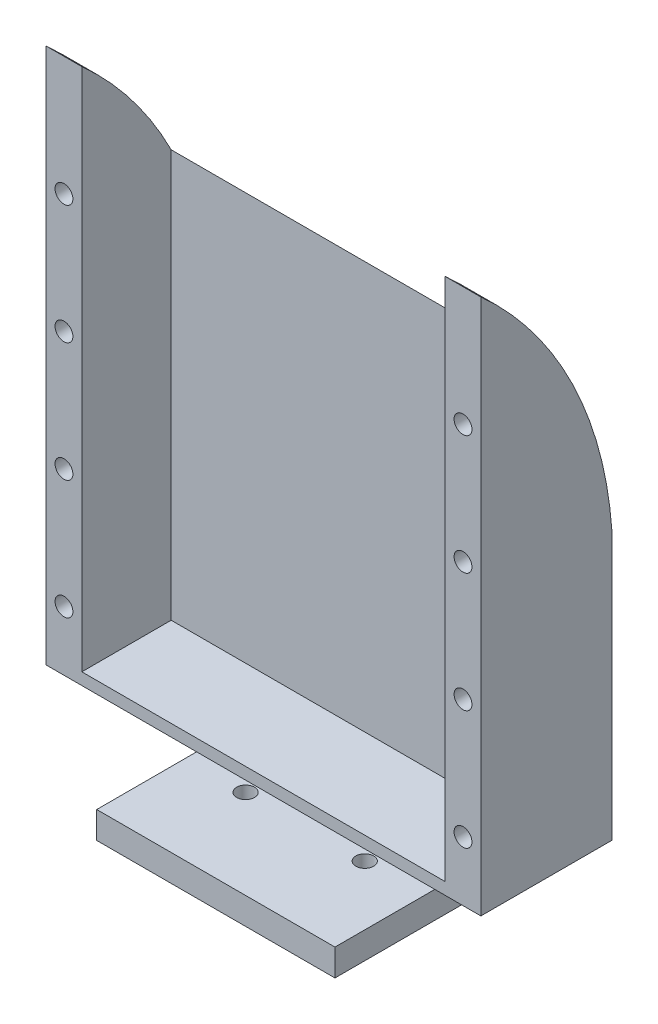
SolidWorks part; units mm, degrees
ref_plane "前视基准面" through (0, 0, 0) normal (0, 0, 1) x (1, 0, 0)
ref_plane "上视基准面" through (0, 0, 0) normal (0, 1, 0) x (1, 0, 0)
ref_plane "右视基准面" through (0, 0, 0) normal (1, 0, 0) x (0, 0, -1)
sketch "草图1" plane through (0, 0, 0) normal (0, 1, 0) x (1, 0, 0)
  line L0 (-10, 0) -> (10, 0) construction
  line L1 (-20, -15) -> (20, -15)
  line L2 (-20, -15) -> (-20, 15)
  line L3 (-20, 15) -> (20, 15)
  line L4 (20, -15) -> (20, 15)
  line L5 (-20, -15) -> (20, 15) construction
  line L6 (-20, 15) -> (20, -15) construction
  circle A2 centre (-10, 0) radius 1.5
  circle A3 centre (10, 0) radius 1.5
  point P0 (0, 0)
  point P9 (0, 0)
  dimension "D3" = 20
  dimension "D4" = 3
  dimension "D5" = 3
  dimension "D1" = 40
  dimension "D2" = 30
extrude "凸台-拉伸1" add sketch "草图1" along normal blind 4.5
sketch "草图2" plane through (0, 4.5, 0) normal (0, 1, 0) x (1, 0, 0)
  circle A0 centre (-10, 0) radius 3.5
  circle A1 centre (10, 0) radius 3.5
  dimension "D1" = 7
  dimension "D2" = 7
sketch "草图3" plane through (0, 0, -15) normal (0, 0, -1) x (-1, 0, 0)
  line L0 (0, 4.5) -> (0, 103.27) construction
  line L2 (-20, 4.5) -> (-20, 13.27)
  line L4 (20, 4.5) -> (20, 13.27)
  line L5 (0, 20.77) -> (0, 0) construction
  line L6 (-10, 8.27) -> (10, 8.27) construction
  line L7 (-20, 4.5) -> (20, 4.5) construction
  line L8 (-20, 4.5) -> (20, 4.5)
  line L9 (-36.5, 13.27) -> (-20, 13.27) construction
  line L10 (20, 13.27) -> (27.5, 13.27) construction
  line L11 (-36.5, 13.27) -> (-20, 13.27)
  line L12 (-36.5, 13.27) -> (-36.5, 103.27)
  line L13 (-36.5, 103.27) -> (36.5, 103.27)
  line L14 (36.5, 13.27) -> (36.5, 103.27)
  line L15 (20, 13.27) -> (36.5, 13.27)
  circle A0 centre (-10, 8.27) radius 1.5
  circle A1 centre (10, 8.27) radius 1.5
  point P11 (0, 8.27)
  point P20 (0, 20.77)
  dimension "D4" = 3
  dimension "D5" = 3
  dimension "D1" = 5
  dimension "D2" = 20
  dimension "D3" = 3.77
  dimension "D7" = 90
  dimension "D8" = 73
extrude "凸台-拉伸2" add sketch "草图3" against normal blind 7
sketch "草图4" plane through (0, 0, -8) normal (0, 0, 1) x (1, 0, 0)
  circle A0 centre (-10, 8.27) radius 3.5
  circle A1 centre (10, 8.27) radius 3.5
  dimension "D1" = 7
  dimension "D2" = 7
extrude "切除-拉伸2" cut sketch "草图4" against normal blind 3
sketch "草图6" plane through (0, 0, -8) normal (0, 0, 1) x (1, 0, 0)
  line L0 (-36.5, 103.27) -> (-36.5, 13.27)
  line L1 (-36.5, 13.27) -> (36.5, 13.27)
  line L2 (36.5, 13.27) -> (36.5, 103.27)
  line L3 (-30.5, 103.27) -> (-30.5, 15.27)
  line L4 (-36.5, 103.27) -> (36.5, 103.27) construction
  line L5 (30.5, 103.27) -> (30.5, 15.27)
  line L6 (-36.5, 103.27) -> (-30.5, 103.27)
  line L7 (30.5, 103.27) -> (36.5, 103.27)
  line L8 (-30.5, 15.27) -> (30.5, 15.27)
  dimension "D1" = 6
  dimension "D2" = 6
  dimension "D3" = 2
extrude "凸台-拉伸3" add sketch "草图6" along normal blind 15
sketch "草图7" plane through (0, 0, 7) normal (0, 0, 1) x (1, 0, 0)
  line L0 (-33.5, 103.27) -> (-33.5, 13.27) construction
  line L1 (-30.5, 103.27) -> (-36.5, 103.27) construction
  line L2 (-36.5, 13.27) -> (36.5, 13.27) construction
  line L3 (33.5, 103.27) -> (33.5, 13.27) construction
  line L4 (36.5, 103.27) -> (30.5, 103.27) construction
  line L5 (-36.5, 83.27) -> (36.5, 83.27) construction
  line L6 (-36.5, 103.27) -> (-36.5, 13.27) construction
  line L7 (36.5, 13.27) -> (36.5, 103.27) construction
  line L8 (-30.5, 103.27) -> (30.5, 103.27) construction
  line L9 (0, 103.27) -> (0, 25.387) construction
  line L10 (-36.5, 63.27) -> (36.5, 63.27) construction
  line L11 (-36.5, 43.27) -> (36.5, 43.27) construction
  line L12 (-36.5, 23.27) -> (36.5, 23.27) construction
  circle A0 centre (-33.5, 83.27) radius 1.5
  circle A1 centre (-33.5, 63.27) radius 1.5
  circle A2 centre (-33.5, 43.27) radius 1.5
  circle A5 centre (33.5, 43.27) radius 1.5
  circle A6 centre (33.5, 63.27) radius 1.5
  circle A7 centre (33.5, 83.27) radius 1.5
  circle A8 centre (-33.5, 23.27) radius 1.5
  circle A9 centre (33.5, 23.27) radius 1.5
  dimension "D5" = 3
  dimension "D1" = 20
  dimension "D2" = 20
  dimension "D3" = 40
  dimension "D4" = 60
extrude "切除-拉伸3" cut sketch "草图7" against normal blind 8
sketch "草图8" plane through (36.5, 0, 0) normal (1, 0, 0) x (0, 0, -1)
  line L0 (4, 103.27) -> (4, 13.27) construction
  line L1 (-7, 103.27) -> (15, 103.27) construction
  line L2 (-7, 13.27) -> (15, 13.27) construction
  circle A0 centre (4, 93.27) radius 1.5
  circle A1 centre (4, 83.27) radius 1.5
  circle A2 centre (4, 73.27) radius 1.5
  circle A3 centre (4, 63.27) radius 1.5
  circle A4 centre (4, 53.27) radius 1.5
  circle A5 centre (4, 43.27) radius 1.5
  circle A6 centre (4, 33.27) radius 1.5
  circle A7 centre (4, 23.27) radius 1.5
  dimension "D1" = 3
  dimension "D3" = 10
  dimension "D4" = 10
  dimension "D5" = 10
  dimension "D6" = 10
  dimension "D7" = 10
  dimension "D8" = 10
  dimension "D9" = 10
  dimension "D2" = 10
sketch "草图9" plane through (-36.5, 0, 0) normal (-1, 0, 0) x (0, 0, 1)
  line L1 (-15, 13.27) -> (-15, 103.27) construction
  line L2 (-15, 58.27) -> (-15, 103.27)
  line L3 (-15, 103.27) -> (7, 103.27)
  arc A0 (7, 103.27) -> (-15, 58.27) centre (51.5574, 53.6086) ccw
extrude "切除-拉伸4" cut sketch "草图9" against normal through all
